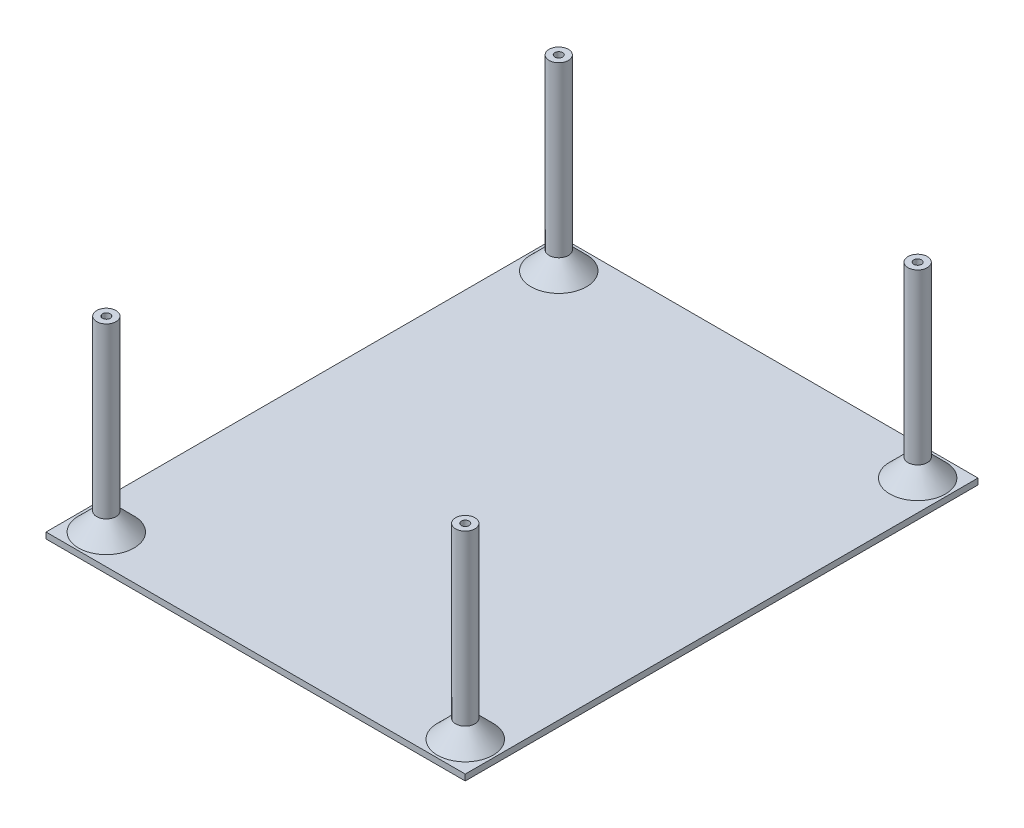
SolidWorks part; units mm, degrees
ref_plane "Спереди" through (0, 0, 0) normal (0, 0, 1) x (1, 0, 0)
ref_plane "Сверху" through (0, 0, 0) normal (0, 1, 0) x (1, 0, 0)
ref_plane "Справа" through (0, 0, 0) normal (1, 0, 0) x (0, 0, -1)
sketch "Эскиз1" plane through (0, 0, 0) normal (0, 1, 0) x (1, 0, 0)
  line L1 (-28.6507, 32.8068) -> (40.8493, 32.8068)
  line L2 (-28.6507, 32.8068) -> (-28.6507, -52.1932)
  line L3 (-28.6507, -52.1932) -> (40.8493, -52.1932)
  line L4 (40.8493, 32.8068) -> (40.8493, -52.1932)
  dimension "D1" = 85
  dimension "D2" = 69.5
extrude "Бобышка-Вытянуть1" add sketch "Эскиз1" along normal blind 1
sketch "Эскиз2" plane through (0, 1, 0) normal (0, 1, 0) x (1, 0, 0)
  line L0 (40.8493, 32.8068) -> (-28.6507, 32.8068) construction
  line L1 (-28.6507, 32.8068) -> (-28.6507, -52.1932) construction
  line L2 (40.8493, -52.1932) -> (40.8493, 32.8068) construction
  line L3 (-28.6507, -52.1932) -> (40.8493, -52.1932) construction
  circle A0 centre (-23.6507, 27.8068) radius 1.6
  circle A1 centre (35.8493, 27.8068) radius 1.6
  circle A2 centre (35.8493, -47.1932) radius 1.6
  circle A3 centre (-23.6507, -47.1932) radius 1.6
  dimension "D1" = 5
  dimension "D2" = 5
  dimension "D3" = 5
  dimension "D4" = 5
  dimension "D5" = 5
  dimension "D6" = 5
  dimension "D7" = 5
  dimension "D8" = 5
extrude "Бобышка-Вытянуть2" add sketch "Эскиз2" along normal blind 31
sketch "Эскиз3" plane through (0, 32, 0) normal (0, 1, 0) x (1, 0, 0)
  circle A0 centre (-23.6507, -47.1932) radius 0.65
  circle A2 centre (-23.6507, -47.1932) radius 1.6 construction
  circle A3 centre (35.8493, -47.1932) radius 0.65
  circle A4 centre (35.8493, -47.1932) radius 1.6 construction
  circle A5 centre (35.8493, 27.8068) radius 0.65
  circle A6 centre (35.8493, 27.8068) radius 1.6 construction
  circle A7 centre (-23.6507, 27.8068) radius 0.65
  circle A8 centre (-23.6507, 27.8068) radius 1.6 construction
  dimension "D1" = 0
  dimension "D2" = 0
  dimension "D3" = 0
  dimension "D4" = 0
  dimension "D5" = 0
  dimension "D6" = 0
extrude "Вырез-Вытянуть1" cut sketch "Эскиз3" against normal blind 5
chamfer "Фаска1" distance 3 angle 45 4 edges at (-23.6507, 1, -26.2068) (35.8493, 1, -26.2068) (-23.6507, 1, 48.7932) (35.8493, 1, 48.7932)
equation "\"D2@Эскиз2\"=\"D1@Эскиз2\""
equation "\"D8@Эскиз2\"=\"D1@Эскиз2\""
equation "\"D7@Эскиз2\"=\"D1@Эскиз2\""
equation "\"D5@Эскиз2\"=\"D1@Эскиз2\""
equation "\"D6@Эскиз2\"=\"D1@Эскиз2\""
equation "\"D4@Эскиз2\"=\"D1@Эскиз2\""
equation "\"D3@Эскиз2\"=\"D1@Эскиз2\""
